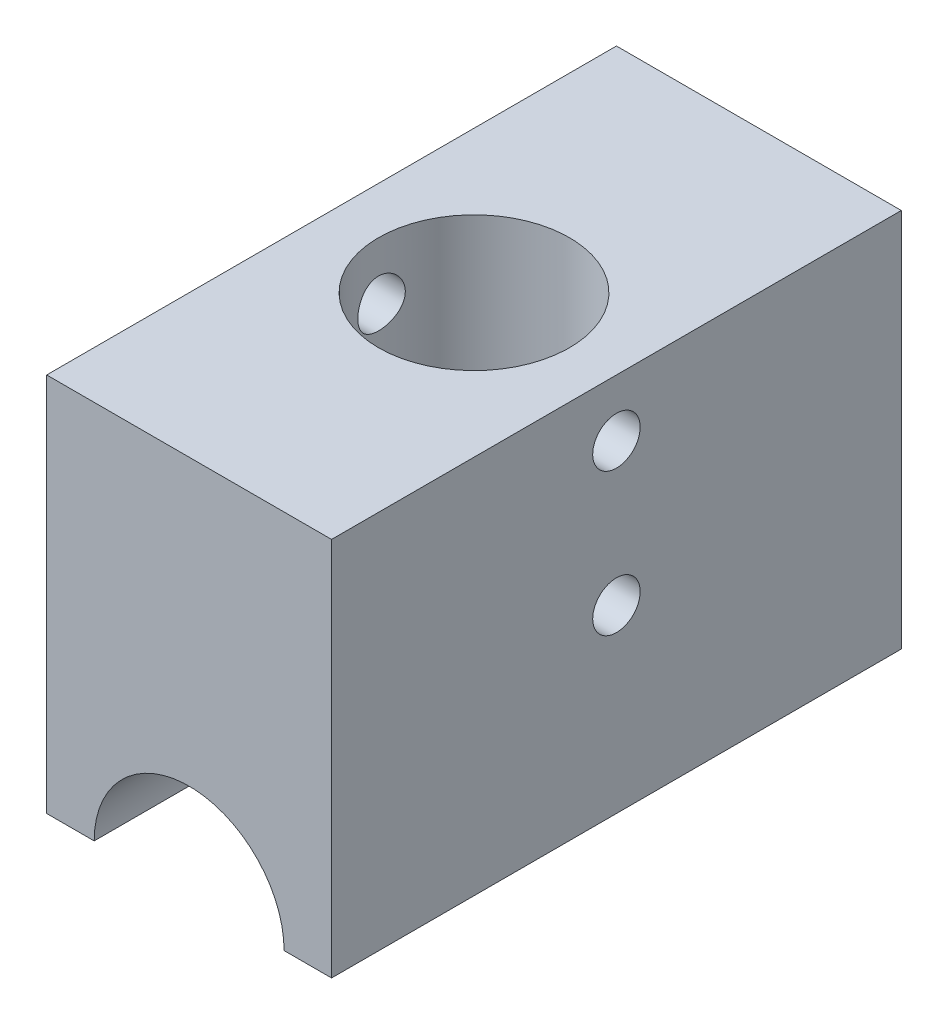
SolidWorks part; units mm, degrees
material "6061-T6 (SS)"
ref_plane "Front Plane" through (0, 0, 0) normal (0, 0, 1) x (1, 0, 0)
ref_plane "Top Plane" through (0, 0, 0) normal (0, 1, 0) x (1, 0, 0)
ref_plane "Right Plane" through (0, 0, 0) normal (1, 0, 0) x (0, 0, -1)
sketch "Sketch1" plane through (0, 0, 0) normal (0, 0, 1) x (1, 0, 0)
  line L1 (-19.05, 25.4) -> (19.05, 25.4)
  line L2 (-19.05, 25.4) -> (-19.05, -25.4)
  line L3 (-19.05, -25.4) -> (19.05, -25.4)
  line L4 (19.05, 25.4) -> (19.05, -25.4)
  line L5 (-19.05, 25.4) -> (19.05, -25.4) construction
  line L6 (-19.05, -25.4) -> (19.05, 25.4) construction
  point P0 (0, 0)
  dimension "D1" = 50.8
  dimension "D2" = 38.1
extrude "Boss-Extrude1" add sketch "Sketch1" along normal blind 76.2
sketch "Sketch2" plane through (19.05, 0, 0) normal (1, 0, 0) x (0, 0, -1)
  line L0 (-76.2, -25.4) -> (0, -25.4)
  arc A0 (-76.2, -25.4) -> (0, -25.4) centre (-38.1, -820.5873) cw
  dimension "D1" = 796.0995
extrude "Cut-Extrude1" [suppressed] cut sketch "Sketch2" against normal through all
ref_plane "Plane1" through (0, 0, 38.1) normal (0, 0, -1) x (-1, 0, 0)
sketch "Sketch3" plane through (0, 0, 38.1) normal (0, 0, -1) x (-1, 0, 0)
  line L0 (0, 806.45) -> (0, 1602.5495) construction
  line L1 (0, 806.45) -> (254, 806.45) construction
  line L2 (0, 806.45) -> (0, 0) construction
  circle A0 centre (0, 1602.5495) radius 12.7
  dimension "D1" = 25.4
  dimension "D2" = 796.0995
  dimension "D3" = 806.45
  dimension "D4" = 254
revolve "Cut-Revolve1" [suppressed] cut sketch "Sketch3" angle 360 about L1
sketch "Sketch4" plane through (0, 25.4, 0) normal (0, 1, 0) x (1, 0, 0)
  line L1 (19.05, 0) -> (-19.05, 0)
  line L2 (19.05, 0) -> (19.05, -76.2)
  line L3 (19.05, -76.2) -> (-19.05, -76.2)
  line L4 (-19.05, 0) -> (-19.05, -76.2)
extrude "Cut-Extrude2" [suppressed] cut sketch "Sketch4" against normal blind 12.7
sketch "Sketch5" plane through (0, 0, 0) normal (0, 0, -1) x (-1, 0, 0)
  line L0 (19.05, -25.4) -> (-19.05, -25.4) construction
  circle A0 centre (0, -25.4) radius 12.7
  dimension "D1" = 25.4
extrude "Cut-Extrude3" cut sketch "Sketch5" against normal through all
sketch "Sketch6" plane through (0, 25.4, 0) normal (0, 1, 0) x (1, 0, 0)
  line L0 (0, 0) -> (0, -76.2) construction
  line L1 (19.05, 0) -> (-19.05, 0) construction
  line L2 (19.05, -76.2) -> (-19.05, -76.2) construction
  circle A0 centre (0, -38.1) radius 12.7635
  dimension "D1" = 25.527
extrude "Cut-Extrude4" cut sketch "Sketch6" against normal blind 50.8
sketch "Sketch7" plane through (19.05, 0, 0) normal (1, 0, 0) x (0, 0, -1)
  line L0 (-38.1, 25.4) -> (-38.1, -25.4) construction
  line L1 (-76.2, 25.4) -> (0, 25.4) construction
  line L2 (-76.2, -25.4) -> (0, -25.4) construction
  circle A0 centre (-38.1, 17.78) radius 3.175
  circle A1 centre (-38.1, -1.27) radius 3.175
  dimension "D1" = 6.35
  dimension "D2" = 7.62
  dimension "D3" = 19.05
extrude "Cut-Extrude5" cut sketch "Sketch7" against normal through all
